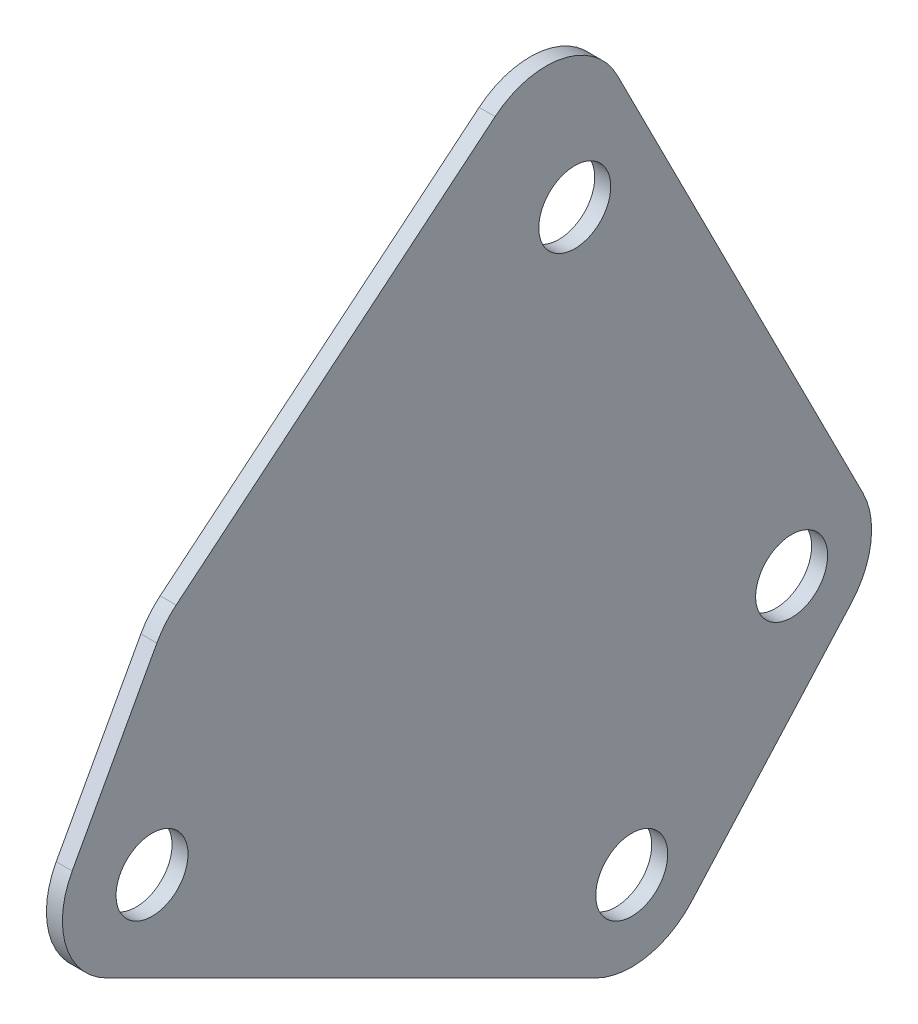
SolidWorks part; units mm, degrees
ref_plane "Front Plane" through (0, 0, 0) normal (0, 0, 1) x (1, 0, 0)
ref_plane "Top Plane" through (0, 0, 0) normal (0, 1, 0) x (1, 0, 0)
ref_plane "Right Plane" through (0, 0, 0) normal (1, 0, 0) x (0, 0, -1)
sketch "Sketch1" plane through (0, 0, 0) normal (1, 0, 0) x (0, 0, -1)
  line L0 (0, 0) -> (30, -15) construction
  line L1 (30, -15) -> (40, -3.8197) construction
  line L2 (40, -3.8197) -> (26.4353, 22.9385) construction
  line L3 (26.4353, 22.9385) -> (0, 0) construction
  line L4 (-2.8423, -4.169) -> (27.7639, -19.4721)
  line L5 (33.7268, -18.3333) -> (43.7268, -7.153)
  line L6 (44.4597, -1.5589) -> (29.0993, 28.7416)
  line L7 (46.0046, -4.6063) -> (30.895, 25.1993) construction
  line L8 (-2.2361, -4.4721) -> (31.1803, -21.1803) construction
  line L9 (-4.9942, 2.7002) -> (0.3029, 12.397)
  line L10 (1.5063, 13.8547) -> (21.455, 30.3355)
  line L11 (31.1803, -21.1803) -> (46.0046, -4.6063) construction
  circle A0 centre (30, -15) radius 2.25
  circle A1 centre (40, -3.8197) radius 2.25
  circle A2 centre (0, 0) radius 2.25
  circle A3 centre (26.4353, 22.9385) radius 2.25
  arc A4 (0.3029, 12.397) -> (1.5063, 13.8547) centre (4.6909, 10) cw
  arc A5 (33.7268, -18.3333) -> (27.7639, -19.4721) centre (30, -15) cw
  arc A6 (43.7268, -7.153) -> (44.4597, -1.5589) centre (40, -3.8197) ccw
  arc A7 (29.0993, 28.7416) -> (21.455, 30.3355) centre (24.6396, 26.4808) ccw
  arc A8 (-4.9942, 2.7002) -> (-2.8423, -4.169) centre (-0.6062, 0.3031) ccw
  point P22 (0.7643, 13.2417)
  dimension "D6" = 4.5
  dimension "D9" = 5
  dimension "D1" = 15
  dimension "D2" = 30
  dimension "D3" = 30
  dimension "D4" = 35
  dimension "D5" = 15
  dimension "D7" = 40
  dimension "D10" = 10
  dimension "D8" = 5
extrude "Boss-Extrude1" add sketch "Sketch1" along normal mid plane 1
